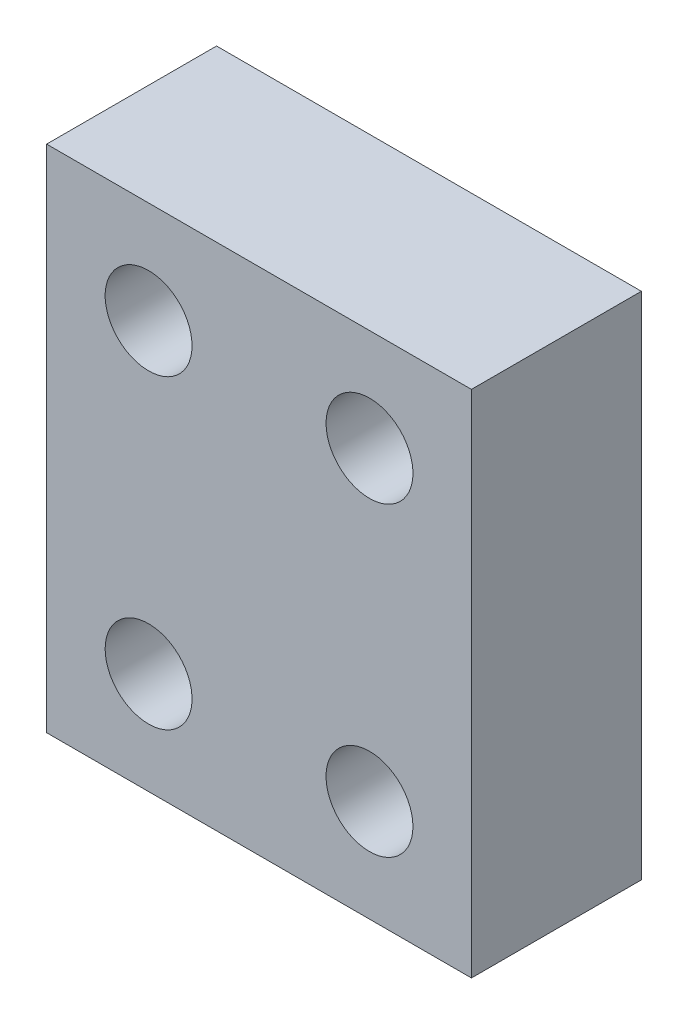
SolidWorks part; units mm, degrees
ref_plane "Front Plane" through (0, 0, 0) normal (0, 0, 1) x (1, 0, 0)
ref_plane "Top Plane" through (0, 0, 0) normal (0, 1, 0) x (1, 0, 0)
ref_plane "Right Plane" through (0, 0, 0) normal (1, 0, 0) x (0, 0, -1)
sketch "Sketch1" plane through (0, 0, 0) normal (0, 0, 1) x (1, 0, 0)
  line L0 (-25, 0) -> (0, 30) construction
  line L1 (0, 0) -> (-25, 0)
  line L2 (0, 0) -> (0, 30)
  line L3 (0, 30) -> (-25, 30)
  line L4 (-25, 0) -> (-25, 30)
  line L5 (-12.5, 15) -> (0, 15) construction
  line L6 (-12.5, 15) -> (-12.5, 30) construction
  line L7 (-19, 24) -> (-19, 30) construction
  line L8 (-19, 24) -> (-25, 24) construction
  circle A0 centre (-19, 24) radius 2.5568
  circle A5 centre (-6, 24) radius 2.5568
  circle A6 centre (-6, 6) radius 2.5568
  circle A7 centre (-19, 6) radius 2.5568
  point P7 (-12.5, 15)
  point P10 (-17.1603, 22.5607)
  point P20 (-19.1944, 24.1944)
  dimension "D3" = 5.1137
  dimension "D1" = 30
  dimension "D2" = 25
  dimension "D4" = 6
extrude "Boss-Extrude1" add sketch "Sketch1" along normal blind 10
equation "\"D3@Sketch1\"=4.917*1.04"
